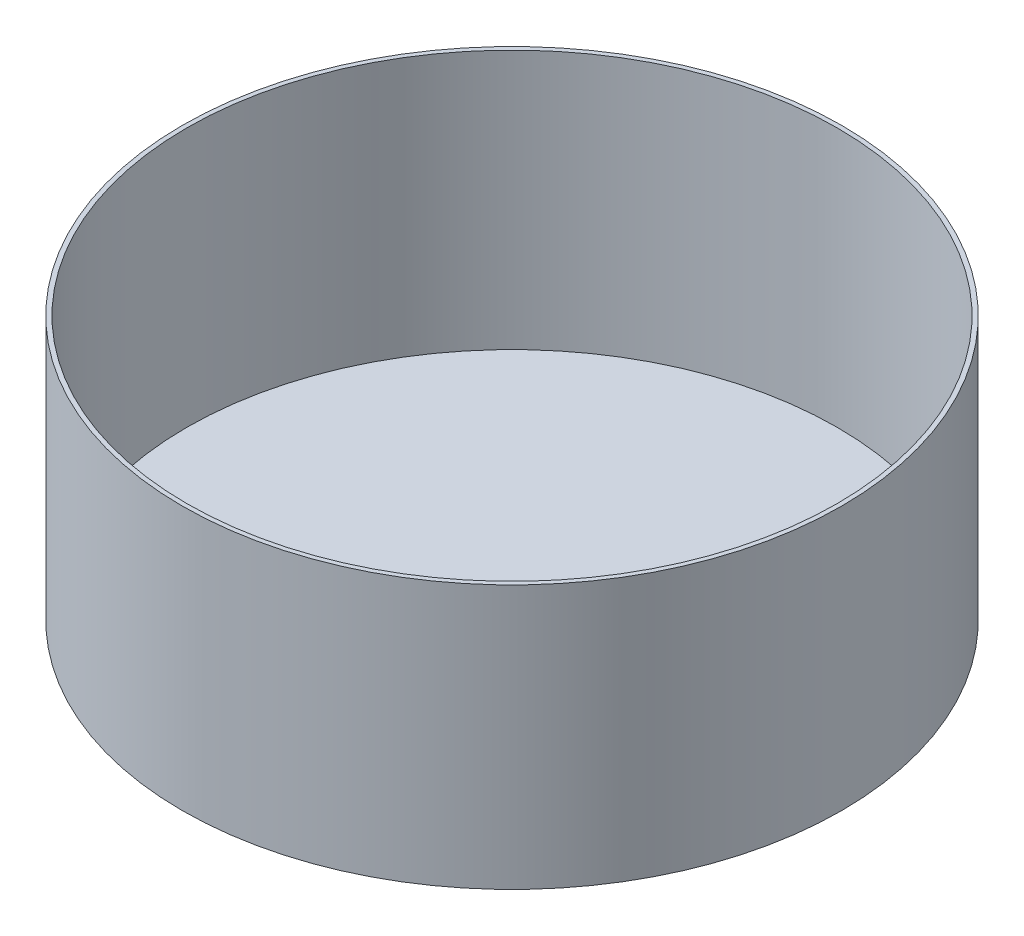
SolidWorks part; units mm, degrees
other "COLLMESH-Shell1"
ref_plane "Piano frontale" through (0, 0, 0) normal (0, 0, 1) x (1, 0, 0)
ref_plane "Piano superiore" through (0, 0, 0) normal (0, 1, 0) x (1, 0, 0)
ref_plane "Piano destro" through (0, 0, 0) normal (1, 0, 0) x (0, 0, -1)
sketch "Sketch1" plane through (0, 0, 0) normal (0, 1, 0) x (1, 0, 0)
  circle A0 centre (0, 0) radius 750
  dimension "D1" = 1500
extrude "Boss-Extrude1" add sketch "Sketch1" along normal blind 600
shell "Shell1" thickness 10
